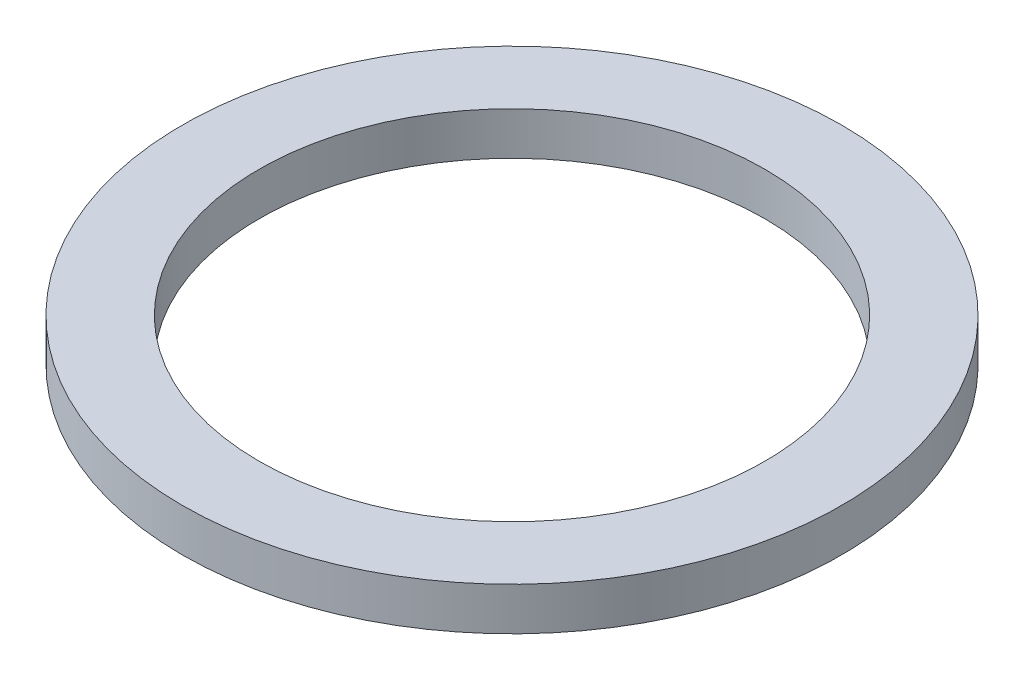
SolidWorks part; units mm, degrees
ref_plane "Front Plane" through (0, 0, 0) normal (0, 0, 1) x (1, 0, 0)
ref_plane "Top Plane" through (0, 0, 0) normal (0, 1, 0) x (1, 0, 0)
ref_plane "Right Plane" through (0, 0, 0) normal (1, 0, 0) x (0, 0, -1)
sketch "Sketch1" plane through (0, 0, 0) normal (0, 1, 0) x (1, 0, 0)
  circle A0 centre (0, 0) radius 21.5
  circle A1 centre (0, 0) radius 16.5
  dimension "D1" = 43
  dimension "D2" = 33
extrude "Boss-Extrude1" add sketch "Sketch1" along normal blind 2.8 contours A0 A1
